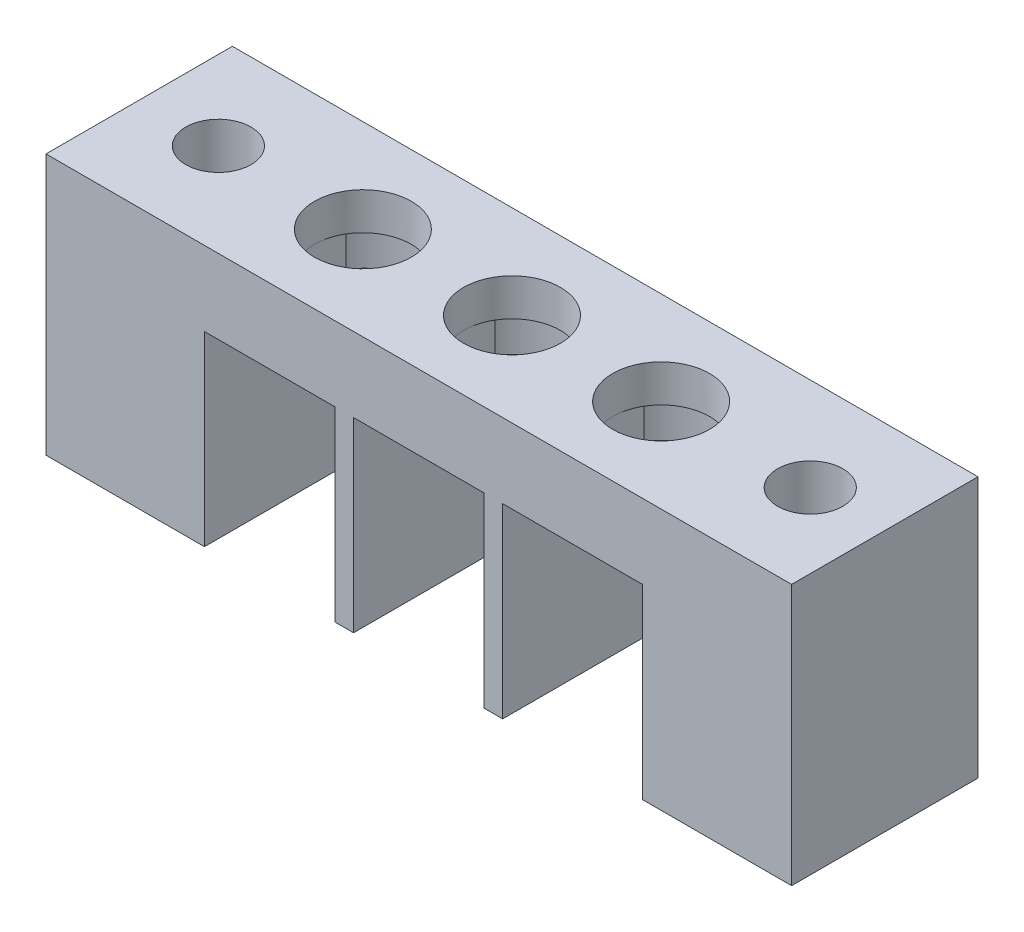
SolidWorks part; units mm, degrees
ref_plane "Płaszczyzna przednia" through (0, 0, 0) normal (0, 0, 1) x (1, 0, 0)
ref_plane "Płaszczyzna górna" through (0, 0, 0) normal (0, 1, 0) x (1, 0, 0)
ref_plane "Płaszczyzna prawa" through (0, 0, 0) normal (1, 0, 0) x (0, 0, -1)
sketch "Sketch1" plane through (0, 0, 0) normal (0, 1, 0) x (1, 0, 0)
  line L1 (-17, -7.3826) -> (15, -7.3826)
  line L2 (-17, -7.3826) -> (-17, 2.6174)
  line L3 (-17, 2.6174) -> (15, 2.6174)
  line L4 (15, -7.3826) -> (15, 2.6174)
  dimension "D1" = 32
  dimension "D2" = 10
extrude "Boss-Extrude1" add sketch "Sketch1" along normal blind 4
sketch "Sketch2" plane through (0, 4, 0) normal (0, 1, 0) x (1, 0, 0)
  line L0 (-17, -2.3826) -> (15, -2.3826) construction
  line L1 (-17, 2.6174) -> (-17, -7.3826) construction
  line L2 (15, -7.3826) -> (15, 2.6174) construction
  line L3 (15, -2.3826) -> (7, -2.3826) construction
  line L4 (7, -2.3826) -> (-1, -2.3826) construction
  line L5 (-1, -2.3826) -> (-9, -2.3826) construction
  line L6 (-9, -2.3826) -> (-17, -2.3826) construction
  circle A1 centre (-9, -2.3826) radius 2.6
  circle A2 centre (-1, -2.3826) radius 2.6
  circle A3 centre (7, -2.3826) radius 2.6
  dimension "D5" = 0
  dimension "D1" = 8
  dimension "D2" = 8
  dimension "D3" = 8
  dimension "D4" = 8
extrude "Cut-Extrude1" cut sketch "Sketch2" against normal blind 10
sketch "Sketch3" plane through (0, 0, 0) normal (0, -1, 0) x (1, 0, 0)
  line L2 (-11.6, 4.0707) -> (-11.6, 0.6944)
  line L4 (-3.6, 4.0707) -> (-3.6, 0.6944)
  line L6 (4.4, 4.0707) -> (4.4, 0.6944)
  arc A1 (-11.6, 0.6944) -> (-11.6, 4.0707) centre (-9, 2.3826) ccw
  arc A2 (-3.6, 0.6944) -> (-3.6, 4.0707) centre (-1, 2.3826) ccw
  arc A3 (4.4, 0.6944) -> (4.4, 4.0707) centre (7, 2.3826) ccw
extrude "Cut-Extrude4" cut sketch "Sketch3" against normal blind 2
sketch "Sketch5" plane through (0, 0, 0) normal (0, -1, 0) x (1, 0, 0)
  line L0 (15, 7.3826) -> (15, -2.6174) construction
  line L5 (-17, -2.6174) -> (15, -2.6174)
  line L10 (-17, -2.6174) -> (-17, -1.6174)
  line L17 (-13, -1.6174) -> (-13.5, -1.6174)
  line L50 (15, -2.6174) -> (15, -1.6174)
  line L59 (-17, 2.8826) -> (-13.5, 2.8826) construction
  line L60 (-17, 7.3826) -> (-13, 7.3826)
  line L61 (-17, 7.3826) -> (-17, -1.6174)
  line L64 (15, 7.3826) -> (11, 7.3826)
  line L65 (15, 7.3826) -> (15, -1.6174)
  line L67 (11, 7.3826) -> (11, -1.6174)
  line L68 (-13.5, 2.8826) -> (-13.5, 7.3826) construction
  line L69 (-17, 7.3826) -> (15, 7.3826) construction
  line L70 (-13.5, 7.3826) -> (-13.5, -1.6174) construction
  line L71 (-13.5, 2.8826) -> (-5.5, 2.8826) construction
  line L72 (-5.5, 2.8826) -> (-5.5, 7.3826) construction
  line L73 (-5.5, 7.3826) -> (-5.5, -1.6174) construction
  line L74 (-5.5, 2.8826) -> (2.5, 2.8826) construction
  line L75 (2.5, 2.8826) -> (2.5, 7.3826) construction
  line L76 (2.5, 7.3826) -> (2.5, -1.6174) construction
  line L77 (-12.5, -1.6174) -> (-5.5, -1.6174)
  line L79 (-13.5, -1.6174) -> (-13.5, 7.3826)
  line L80 (-13.5, 7.3826) -> (-12.5, 7.3826)
  line L81 (-12.5, -1.6174) -> (-12.5, 7.3826)
  line L83 (-5.5, -1.6174) -> (-5.5, 7.3826)
  line L84 (-5.5, 7.3826) -> (-4.5, 7.3826)
  line L85 (-4.5, -1.6174) -> (-4.5, 7.3826)
  line L87 (2.5, -1.6174) -> (2.5, 7.3826)
  line L88 (2.5, 7.3826) -> (3.5, 7.3826)
  line L89 (3.5, -1.6174) -> (3.5, 7.3826)
  line L90 (-4.5, -1.6174) -> (2.5, -1.6174)
  line L91 (3.5, -1.6174) -> (11, -1.6174)
  dimension "D1" = 1
  dimension "D2" = 4
  dimension "D3" = 4
  dimension "D4" = 1
  dimension "D5" = 1
  dimension "D6" = 1
extrude "Boss-Extrude4" add sketch "Sketch5" along normal blind 10
sketch "Sketch9" plane through (15, 0, 0) normal (1, 0, 0) x (0, 0, -1)
  line L1 (-7.3826, 4) -> (2.6174, 4)
  line L2 (-7.3826, 4) -> (-7.3826, -10)
  line L3 (-7.3826, -10) -> (2.6174, -10)
  line L4 (2.6174, 4) -> (2.6174, -10)
extrude "Boss-Extrude5" add sketch "Sketch9" along normal blind 4
sketch "Sketch10" plane through (-17, 0, 0) normal (-1, 0, 0) x (0, 0, 1)
  line L1 (-2.6174, 4) -> (7.3826, 4)
  line L2 (-2.6174, 4) -> (-2.6174, -10)
  line L3 (-2.6174, -10) -> (7.3826, -10)
  line L4 (7.3826, 4) -> (7.3826, -10)
extrude "Boss-Extrude6" add sketch "Sketch10" along normal blind 4
sketch "Sketch6" plane through (0, -10, 0) normal (0, -1, 0) x (1, 0, 0)
  line L0 (-16.75, 7.3826) -> (-16.75, -2.6174) construction
  line L2 (-21, -2.6174) -> (19, -2.6174) construction
  line L3 (-12.5, 7.3826) -> (-21, 7.3826) construction
  line L4 (-21, 2.3826) -> (-12.5, 2.3826) construction
  line L6 (15, 7.3826) -> (15, -2.6174) construction
  line L7 (19, 7.3826) -> (11, 7.3826) construction
  line L8 (-21, -2.6174) -> (-21, 7.3826) construction
  line L9 (-12.5, -1.6174) -> (-12.5, 7.3826) construction
  line L10 (19, 2.3826) -> (11, 2.3826) construction
  line L11 (19, 7.3826) -> (19, -2.6174) construction
  line L12 (11, 7.3826) -> (11, -1.6174) construction
  line L13 (-21, -2.6174) -> (19, -2.6174) construction
  circle A2 centre (-16.75, 2.3826) radius 1.75
  circle A3 centre (15, 2.3826) radius 1.75
extrude "Cut-Extrude5" cut sketch "Sketch6" against normal blind 40
sketch "Sketch8" plane through (0, -10, 0) normal (0, -1, 0) x (1, 0, 0)
  line L1 (-16.8395, 5.5567) -> (-19.5437, 3.8921)
  line L2 (-19.5437, 3.8921) -> (-19.4541, 0.7179)
  line L3 (-19.4541, 0.7179) -> (-16.6605, -0.7916)
  line L4 (-16.6605, -0.7916) -> (-13.9563, 0.873)
  line L5 (-13.9563, 0.873) -> (-14.0459, 4.0472)
  line L6 (-14.0459, 4.0472) -> (-16.8395, 5.5567)
  line L8 (15, 5.558) -> (12.25, 3.9703)
  line L9 (12.25, 3.9703) -> (12.25, 0.7948)
  line L10 (12.25, 0.7948) -> (15, -0.7929)
  line L11 (15, -0.7929) -> (17.75, 0.7948)
  line L12 (17.75, 0.7948) -> (17.75, 3.9703)
  line L13 (17.75, 3.9703) -> (15, 5.558)
  circle A0 centre (-16.75, 2.3826) radius 2.75 construction
  circle A2 centre (15, 2.3826) radius 2.75 construction
  dimension "D1" = 5.5
  dimension "D3" = 5.5
  dimension "D2" = 6.3483
  dimension "D4" = 6.3509
extrude "Cut-Extrude6" cut sketch "Sketch8" against normal blind 5
